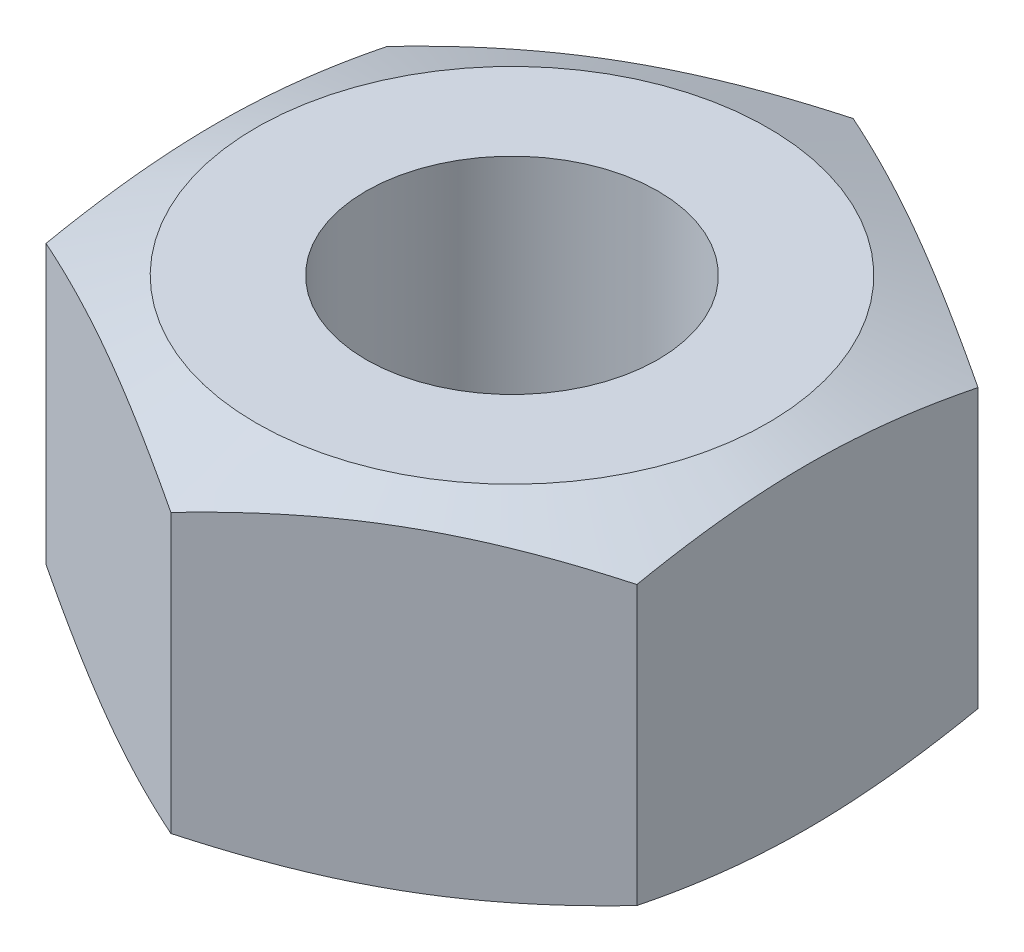
SolidWorks part; units mm, degrees
ref_plane "Front Plane" through (0, 0, 0) normal (0, 0, 1) x (1, 0, 0)
ref_plane "Top Plane" through (0, 0, 0) normal (0, 1, 0) x (1, 0, 0)
ref_plane "Right Plane" through (0, 0, 0) normal (1, 0, 0) x (0, 0, -1)
sketch "Sketch1" plane through (0, 0, 0) normal (0, 1, 0) x (1, 0, 0)
  line L1 (0, 9.815) -> (-8.5, 4.9075)
  line L2 (-8.5, 4.9075) -> (-8.5, -4.9075)
  line L3 (-8.5, -4.9075) -> (0, -9.815)
  line L4 (0, -9.815) -> (8.5, -4.9075)
  line L5 (8.5, -4.9075) -> (8.5, 4.9075)
  line L6 (8.5, 4.9075) -> (0, 9.815)
  circle A0 centre (0, 0) radius 8.5 construction
  circle A1 centre (0, 0) radius 4.2
  dimension "D2" = 8.4
  dimension "D1" = 17
extrude "Boss-Extrude1" add sketch "Sketch1" along normal blind 10
sketch "Sketch2" plane through (0, 0, 0) normal (1, 0, 0) x (0, 0, -1)
  line L0 (-12.9868, 5) -> (12.1674, 5) construction
  line L1 (0, 13.2068) -> (0, -2.6356) construction
  line L2 (-9.815, 9) -> (-7.3612, 10)
  line L3 (-9.815, 10) -> (-9.815, 0) construction
  line L4 (-9.815, 10) -> (-4.9075, 10) construction
  line L5 (-7.3612, 10) -> (-9.815, 10)
  line L6 (-9.815, 10) -> (-9.815, 9)
  line L7 (7.3612, 10) -> (9.815, 10)
  line L8 (9.815, 9) -> (7.3612, 10)
  line L9 (9.815, 10) -> (9.815, 9)
  line L10 (-9.815, 10) -> (-9.815, 9)
  line L11 (-9.815, 9) -> (-7.3612, 10)
  line L12 (-7.3612, 10) -> (-9.815, 10)
  line L13 (9.815, 10) -> (9.815, 9)
  line L14 (7.3612, 10) -> (9.815, 10)
  line L15 (9.815, 9) -> (7.3612, 10)
  line L16 (9.815, 1) -> (7.3612, 0)
  line L17 (7.3612, 0) -> (9.815, 0)
  line L18 (9.815, 0) -> (9.815, 1)
  line L19 (9.815, 0) -> (9.815, 1)
  line L20 (-7.3612, 0) -> (-9.815, 0)
  line L21 (-9.815, 0) -> (-9.815, 1)
  line L22 (-9.815, 1) -> (-7.3612, 0)
  dimension "D1" = 1
  dimension "D2" = 2.4537
revolve "Cut-Revolve1" cut sketch "Sketch2" angle 360 about L1
